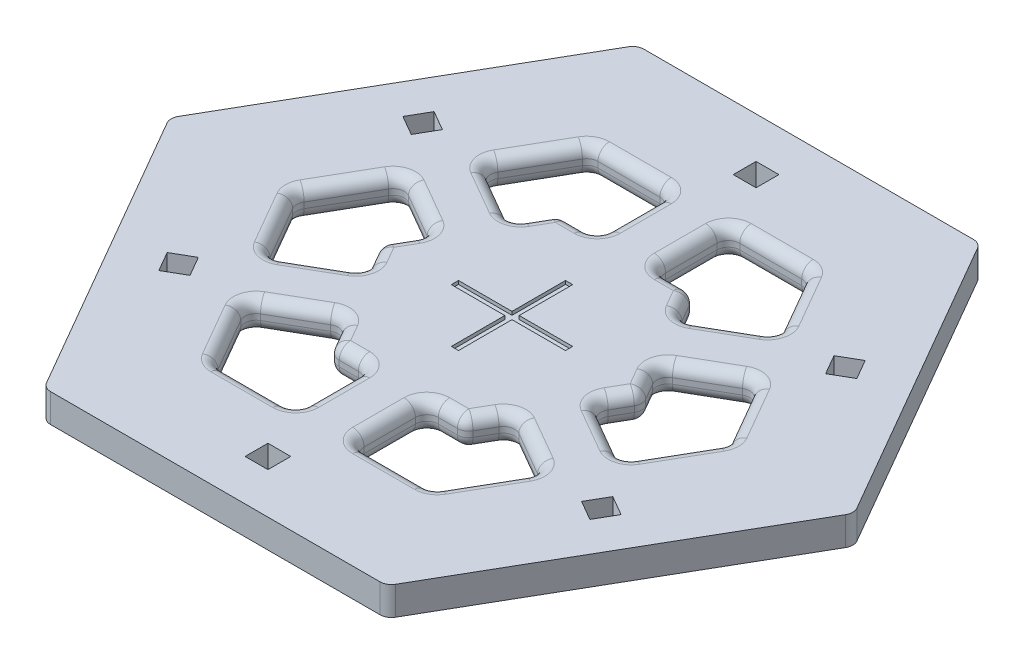
SolidWorks part; units mm, degrees
material "ABS"
ref_plane "Front Plane" through (0, 0, 0) normal (0, 0, 1) x (1, 0, 0)
ref_plane "Top Plane" through (0, 0, 0) normal (0, 1, 0) x (1, 0, 0)
ref_plane "Right Plane" through (0, 0, 0) normal (1, 0, 0) x (0, 0, -1)
sketch "Sketch1" plane through (0, 0, 0) normal (0, 1, 0) x (1, 0, 0)
  line L0 (0, 65.9911) -> (0, -65.9911) construction
  line L1 (76.2, 0) -> (38.1, 65.9911)
  line L2 (38.1, 65.9911) -> (-38.1, 65.9911)
  line L3 (-38.1, 65.9911) -> (-76.2, 0)
  line L4 (-76.2, 0) -> (-38.1, -65.9911)
  line L5 (-38.1, -65.9911) -> (38.1, -65.9911)
  line L6 (38.1, -65.9911) -> (76.2, 0)
  line L7 (48.26, 0) -> (40.64, 13.1982)
  line L8 (24.13, 41.7944) -> (8.89, 41.7944)
  line L9 (-24.13, 41.7944) -> (-31.75, 28.5962)
  line L10 (-48.26, 0) -> (-40.64, -13.1982)
  line L11 (-24.13, -41.7944) -> (-8.89, -41.7944)
  line L12 (24.13, -41.7944) -> (31.75, -28.5962)
  line L13 (29.21, 0) -> (25.0825, 7.149)
  line L14 (14.605, 25.2966) -> (6.35, 25.2966)
  line L15 (-14.605, 25.2966) -> (-18.7325, 18.1476)
  line L16 (-29.21, 0) -> (-25.0825, -7.149)
  line L17 (-14.605, -25.2966) -> (-6.35, -25.2966)
  line L18 (14.605, -25.2966) -> (18.7325, -18.1476)
  line L19 (-30.8203, 25.1265) -> (-18.7325, 18.1476)
  line L20 (-37.1703, 14.1279) -> (-25.0825, 7.149)
  line L21 (37.1703, 14.1279) -> (25.0825, 7.149)
  line L22 (30.8203, 25.1265) -> (18.7325, 18.1476)
  line L23 (-48.26, 0) -> (48.26, 0) construction
  line L24 (48.26, 0) -> (-48.26, 0) construction
  line L25 (37.1703, -14.1279) -> (25.0825, -7.149)
  line L26 (30.8203, -25.1265) -> (18.7325, -18.1476)
  line L27 (-24.13, 41.7944) -> (24.13, -41.7944) construction
  line L28 (-6.35, 39.2544) -> (-6.35, 25.2966)
  line L29 (6.35, 39.2544) -> (6.35, 25.2966)
  line L30 (-30.8203, -25.1265) -> (-18.7325, -18.1476)
  line L31 (-37.1703, -14.1279) -> (-25.0825, -7.149)
  line L32 (6.35, -39.2544) -> (6.35, -25.2966)
  line L33 (-6.35, -39.2544) -> (-6.35, -25.2966)
  line L34 (18.7325, 18.1476) -> (14.605, 25.2966)
  line L35 (-6.35, 25.2966) -> (-14.605, 25.2966)
  line L36 (-8.89, 41.7944) -> (-24.13, 41.7944)
  line L37 (-25.0825, 7.149) -> (-29.21, 0)
  line L38 (-40.64, 13.1982) -> (-48.26, 0)
  line L39 (-31.75, -28.5962) -> (-24.13, -41.7944)
  line L40 (-18.7325, -18.1476) -> (-14.605, -25.2966)
  line L41 (6.35, -25.2966) -> (14.605, -25.2966)
  line L42 (8.89, -41.7944) -> (24.13, -41.7944)
  line L43 (40.64, -13.1982) -> (48.26, 0)
  line L44 (25.0825, -7.149) -> (29.21, 0)
  line L45 (31.75, 28.5962) -> (24.13, 41.7944)
  circle A0 centre (0, 0) radius 65.9911 construction
  circle A1 centre (0, 0) radius 41.7944 construction
  circle A2 centre (0, 0) radius 25.2966 construction
  arc A3 (-31.75, -28.5962) -> (-30.8203, -25.1265) centre (-29.5503, -27.3262) cw
  arc A4 (-37.1703, -14.1279) -> (-40.64, -13.1982) centre (-38.4403, -11.9282) cw
  arc A5 (-40.64, 13.1982) -> (-37.1703, 14.1279) centre (-38.4403, 11.9282) cw
  arc A6 (-31.75, 28.5962) -> (-30.8203, 25.1265) centre (-29.5503, 27.3262) ccw
  arc A7 (-8.89, 41.7944) -> (-6.35, 39.2544) centre (-8.89, 39.2544) cw
  arc A8 (6.35, 39.2544) -> (8.89, 41.7944) centre (8.89, 39.2544) cw
  arc A9 (40.64, -13.1982) -> (37.1703, -14.1279) centre (38.4403, -11.9282) cw
  arc A10 (30.8203, -25.1265) -> (31.75, -28.5962) centre (29.5503, -27.3262) cw
  arc A11 (8.89, -41.7944) -> (6.35, -39.2544) centre (8.89, -39.2544) cw
  arc A12 (-6.35, -39.2544) -> (-8.89, -41.7944) centre (-8.89, -39.2544) cw
  arc A13 (40.64, 13.1982) -> (37.1703, 14.1279) centre (38.4403, 11.9282) ccw
  arc A14 (30.8203, 25.1265) -> (31.75, 28.5962) centre (29.5503, 27.3262) ccw
  point P42 (0, 0)
  point P50 (0, 0)
  point P57 (-33.02, -26.3965)
  point P60 (-39.37, -15.3979)
  point P63 (-39.37, 15.3979)
  point P66 (-33.02, 26.3965)
  point P69 (-6.35, 41.7944)
  point P72 (6.35, 41.7944)
  point P79 (6.35, -41.7944)
  point P82 (-6.35, -41.7944)
  point P85 (39.37, 15.3979)
  point P88 (33.02, 26.3965)
  dimension "D4" = 2.54
  dimension "D5" = 2.54
  dimension "D1" = 76.2
  dimension "D2" = 48.26
  dimension "D3" = 29.21
  dimension "D6" = 2
  dimension "D7" = 2
extrude "Boss-Extrude1" add sketch "Sketch1" along normal blind 6.35
sketch "Sketch3" plane through (0, 6.35, 0) normal (0, 1, 0) x (1, 0, 0)
  line L0 (38.1, 65.9911) -> (-38.1, 65.9911) construction
  line L1 (-2.54, 56.8402) -> (2.54, 56.8402)
  line L2 (-2.54, 56.8402) -> (-2.54, 51.7602)
  line L3 (-2.54, 51.7602) -> (2.54, 51.7602)
  line L4 (2.54, 56.8402) -> (2.54, 51.7602)
  line L5 (47.9551, 30.6198) -> (50.4951, 26.2204)
  line L6 (50.4951, 26.2204) -> (46.0957, 23.6804)
  line L7 (43.5557, 28.0798) -> (46.0957, 23.6804)
  line L8 (47.9551, 30.6198) -> (43.5557, 28.0798)
  line L9 (50.4951, -26.2204) -> (47.9551, -30.6198)
  line L10 (47.9551, -30.6198) -> (43.5557, -28.0798)
  line L11 (46.0957, -23.6804) -> (43.5557, -28.0798)
  line L12 (50.4951, -26.2204) -> (46.0957, -23.6804)
  line L13 (2.54, -56.8402) -> (-2.54, -56.8402)
  line L14 (-2.54, -56.8402) -> (-2.54, -51.7602)
  line L15 (2.54, -51.7602) -> (-2.54, -51.7602)
  line L16 (2.54, -56.8402) -> (2.54, -51.7602)
  line L17 (-47.9551, -30.6198) -> (-50.4951, -26.2204)
  line L18 (-50.4951, -26.2204) -> (-46.0957, -23.6804)
  line L19 (-43.5557, -28.0798) -> (-46.0957, -23.6804)
  line L20 (-47.9551, -30.6198) -> (-43.5557, -28.0798)
  line L21 (0, 65.9911) -> (0, -65.9911) construction
  line L22 (-38.1, -65.9911) -> (38.1, -65.9911) construction
  line L23 (-47.9551, 30.6198) -> (-43.5557, 28.0798)
  line L24 (-47.9551, 30.6198) -> (-50.4951, 26.2204)
  line L25 (-50.4951, 26.2204) -> (-46.0957, 23.6804)
  line L26 (-43.5557, 28.0798) -> (-46.0957, 23.6804)
  line L27 (6.35, 39.2544) -> (6.35, 25.2966) construction
  point P6 (0, 56.8402)
  point P7 (0, 65.9911)
  point P28 (0, 0)
  dimension "D1" = 5.08
  dimension "D2" = 5.08
  dimension "D3" = 9.1509
  dimension "D4" = 38.1
  dimension "D6" = 51.7602
  dimension "D7" = 47.3608
  dimension "D5" = 5
extrude "Cut-Extrude2" cut sketch "Sketch3" against normal blind 62.484
fillet "Fillet1" radius 2.54 120 edges at (10.4775, 6.35, 25.2966) (7.0939, 6.35, 41.0504) (7.0939, 0, 41.0504) (32.0037, 6.35, 26.6688) (32.0037, 0, 26.6688) (-7.0939, 6.35, 41.0504) (-7.0939, 0, 41.0504) (-32.0037, 6.35, 26.6688) (-32.0037, 0, 26.6688) (-39.0977, 6.35, -14.3817) (-39.0977, 0, -14.3817) (-39.0977, 6.35, 14.3817) (-39.0977, 0, 14.3817) (39.0977, 6.35, 14.3817) (39.0977, 0, 14.3817) (39.0977, 6.35, -14.3817) (39.0977, 0, -14.3817) (32.0037, 6.35, -26.6688) (32.0037, 0, -26.6688) (7.0939, 6.35, -41.0504) (7.0939, 0, -41.0504) (-32.0037, 6.35, -26.6688) (-32.0037, 0, -26.6688) (-7.0939, 6.35, -41.0504) (-7.0939, 0, -41.0504) (-31.1264, 6.35, -10.6385) (-31.1264, 0, -10.6385) (-27.1462, 6.35, 3.5745) (-27.1462, 0, 3.5745) (-25.0825, 3.175, -7.149) (-27.1462, 6.35, -3.5745) (-29.21, 3.175, 0) (-27.1462, 0, -3.5745) (-25.0825, 3.175, 7.149) (-31.1264, 6.35, 10.6385) (-31.1264, 0, 10.6385) (6.35, 6.35, 32.2755) (6.35, 3.175, 25.2966) (6.35, 0, 32.2755) (24.7764, 6.35, 21.637) (24.7764, 0, 21.637) (16.51, 6.35, 41.7944) (16.51, 0, 41.7944) (27.94, 6.35, 35.1953) (24.13, 3.175, 41.7944) (27.94, 0, 35.1953) (-27.94, 6.35, 35.1953) (-27.94, 0, 35.1953) (-16.51, 6.35, 41.7944) (-24.13, 3.175, 41.7944) (-16.51, 0, 41.7944) (-6.35, 6.35, 32.2755) (-6.35, 0, 32.2755) (-24.7764, 6.35, 21.637) (-24.7764, 0, 21.637) (-18.7325, 3.175, 18.1476) (-16.6687, 6.35, 21.7221) (-16.6687, 0, 21.7221) (-14.605, 3.175, 25.2966) (-10.4775, 6.35, 25.2966) (-6.35, 3.175, 25.2966) (-10.4775, 0, 25.2966) (-44.45, 6.35, -6.5991) (-44.45, 0, -6.5991) (-44.45, 6.35, 6.5991) (-48.26, 3.175, 0) (-44.45, 0, 6.5991) (14.605, 3.175, 25.2966) (16.6688, 6.35, 21.7221) (18.7325, 3.175, 18.1476) (16.6688, 0, 21.7221) (31.1264, 6.35, 10.6385) (31.1264, 0, 10.6385) (25.0825, 3.175, 7.149) (27.1463, 6.35, 3.5745) (27.1463, 0, 3.5745) (44.45, 6.35, 6.5991) (44.45, 0, 6.5991) (44.45, 6.35, -6.5991) (48.26, 3.175, 0) (44.45, 0, -6.5991) (31.1264, 6.35, -10.6385) (31.1264, 0, -10.6385) (29.21, 3.175, 0) (27.1462, 6.35, -3.5745) (25.0825, 3.175, -7.149) (27.1462, 0, -3.5745) (10.4775, 6.35, -25.2966) (10.4775, 0, -25.2966) (16.6687, 6.35, -21.7221) (14.605, 3.175, -25.2966) (16.6687, 0, -21.7221) (24.7764, 6.35, -21.637) (18.7325, 3.175, -18.1476) (24.7764, 0, -21.637) (27.94, 6.35, -35.1953) (27.94, 0, -35.1953) (16.51, 6.35, -41.7944) (24.13, 3.175, -41.7944) (16.51, 0, -41.7944) (6.35, 3.175, -25.2966) (6.35, 6.35, -32.2755) (6.35, 0, -32.2755) (-24.7764, 6.35, -21.637) (-24.7764, 0, -21.637) (-10.4775, 6.35, -25.2966) (-10.4775, 0, -25.2966) (-14.605, 3.175, -25.2966) (-16.6687, 6.35, -21.7221) (-18.7325, 3.175, -18.1476) (-16.6687, 0, -21.7221) (-6.35, 6.35, -32.2755) (-6.35, 3.175, -25.2966) (-6.35, 0, -32.2755) (-27.94, 6.35, -35.1953) (-27.94, 0, -35.1953) (-24.13, 3.175, -41.7944) (-16.51, 6.35, -41.7944) (-16.51, 0, -41.7944) (10.4775, 0, 25.2966)
fillet "Fillet2" radius 2.54 1 edges at (-38.1, 3.175, 65.9911)
fillet "Fillet3" radius 2.54 1 edges at (38.1, 3.175, 65.9911)
fillet "Fillet4" radius 2.54 1 edges at (76.2, 3.175, 0)
fillet "Fillet5" radius 2.54 1 edges at (38.1, 3.175, -65.9911)
fillet "Fillet6" radius 2.54 1 edges at (-38.1, 3.175, -65.9911)
fillet "Fillet7" radius 2.54 1 edges at (-76.2, 3.175, 0)
sketch "Sketch4" plane through (0, 6.35, 0) normal (0, 1, 0) x (1, 0, 0)
  line L1 (-0.7976, 12.7) -> (0.7976, 12.7)
  line L2 (-0.7976, 12.7) -> (-0.7976, -12.7)
  line L3 (-0.7976, -12.7) -> (0.7976, -12.7)
  line L4 (0.7976, 12.7) -> (0.7976, -12.7)
  line L5 (-0.7976, 12.7) -> (0.7976, -12.7) construction
  line L6 (-0.7976, -12.7) -> (0.7976, 12.7) construction
  line L7 (-12.7, -0.7976) -> (12.7, -0.7976)
  line L8 (-12.7, -0.7976) -> (-12.7, 0.7976)
  line L9 (-12.7, 0.7976) -> (12.7, 0.7976)
  line L10 (12.7, -0.7976) -> (12.7, 0.7976)
  line L11 (-12.7, -0.7976) -> (12.7, 0.7976) construction
  line L12 (-12.7, 0.7976) -> (12.7, -0.7976) construction
  dimension "D1" = 25.4
  dimension "D2" = 12.7
  dimension "D3" = 12.7
  dimension "D4" = 25.4
  dimension "D5" = 0.7976
  dimension "D6" = 0.7976
  dimension "D7" = 0.7976
  dimension "D8" = 0.7976
extrude "Cut-Extrude4" cut sketch "Sketch4" against normal blind 0.762 contours L9 L8 L7 L2 | L7 L2 L3 L4 | L9 L2 L7 L4 | L7 L10 L9 L4 | L2 L9 L4 L1
